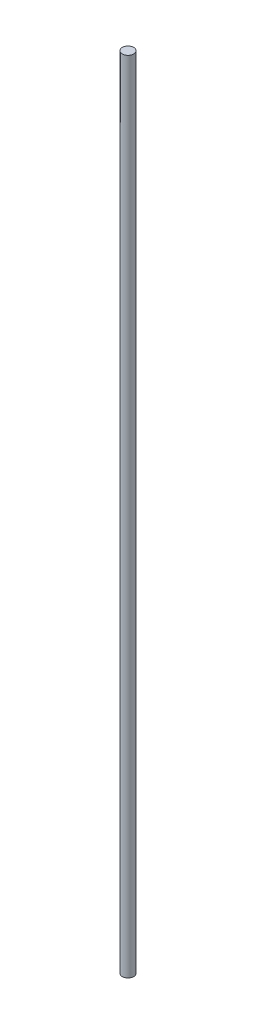
SolidWorks part; units mm, degrees
material "松木"
ref_plane "前视基准面" through (0, 0, 0) normal (0, 0, 1) x (1, 0, 0)
ref_plane "上视基准面" through (0, 0, 0) normal (0, 1, 0) x (1, 0, 0)
ref_plane "右视基准面" through (0, 0, 0) normal (1, 0, 0) x (0, 0, -1)
sketch "草图1" plane through (0, 0, 0) normal (0, 1, 0) x (1, 0, 0)
  circle A0 centre (0, 0) radius 12.5
  dimension "D1" = 25
extrude "凸台-拉伸1" add sketch "草图1" along normal blind 1750
